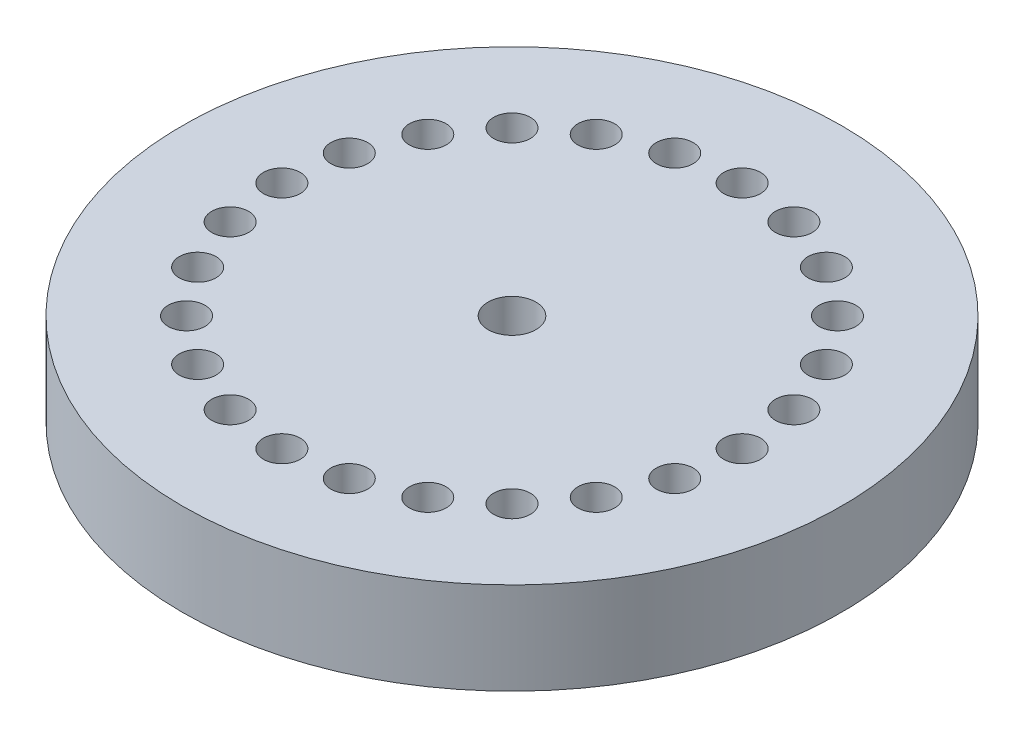
SolidWorks part; units mm, degrees
ref_plane "Front Plane" through (0, 0, 0) normal (0, 0, 1) x (1, 0, 0)
ref_plane "Top Plane" through (0, 0, 0) normal (0, 1, 0) x (1, 0, 0)
ref_plane "Right Plane" through (0, 0, 0) normal (1, 0, 0) x (0, 0, -1)
sketch "Sketch1" plane through (0, 0, 0) normal (0, 1, 0) x (1, 0, 0)
  circle A0 centre (0, 0) radius 20.066 construction
  circle A1 centre (0, 0) radius 45.466
  dimension "D1" = 25.4
extrude "Boss-Extrude1" add sketch "Sketch1" along normal blind 25.4
sketch "Sketch3" plane through (0, 0, 0) normal (0, -1, 0) x (1, 0, 0)
  circle A0 centre (0, 0) radius 20.32
extrude "Cut-Extrude1" cut sketch "Sketch3" against normal blind 12.7
sketch "Sketch4" plane through (0, 0, 0) normal (0, -1, 0) x (1, 0, 0)
  line L0 (0, 0) -> (0, 31.75) construction
  circle A0 centre (0, 31.75) radius 1.778
hole_wizard "CSK for 1/4 Flat Head Machine Screw1" positions "Sketch6" profile "Sketch7" countersink size "1/4" standard "ANSI Inch"
sketch "Sketch6" plane through (0, 25.4, 0) normal (0, 1, 0) x (1, 0, 0)
  point P0 (0, 0)
sketch "Sketch7" plane through (0, 25.4, 0) normal (1, 0, 0) x (0, 0, 1)
  line L0 (0, 0) -> (0, 27.3611)
  line L1 (0, 27.3611) -> (3.2639, 25.4)
  line L2 (3.2639, 25.4) -> (3.2639, 3.6524)
  line L3 (3.2639, 3.6524) -> (6.4389, 0)
  line L5 (6.4389, 0) -> (0, 0)
  line L6 (-3.2639, 3.6524) -> (-6.4389, 0) construction
  line L10 (0, 27.3611) -> (-3.2639, 25.4) construction
  line L11 (0, -6.35) -> (0, 107.95) construction
  dimension "Hole Dia." = 6.5278
  dimension "Hole Depth" = 25.4
  dimension "Near C'Sink Dia." = 12.8778
  dimension "Near C'Sink Angle" = 82
  dimension "Drill Angle" = 118
sketch "Sketch8" plane through (0, 25.4, 0) normal (0, 1, 0) x (1, 0, 0)
  circle A0 centre (0, 0) radius 46.9556
extrude "Cut-Extrude2" cut sketch "Sketch8" against normal blind 12.7
extrude "Cut-Extrude3" cut sketch "Sketch4" against normal through all
sketch "Sketch9" plane through (0, 12.7, 0) normal (0, 1, 0) x (1, 0, 0)
  circle A0 centre (0, -31.75) radius 2.54
extrude "Cut-Extrude4" cut sketch "Sketch9" against normal blind 5.08
pattern_circular "CirPattern1" count 24 every 15 about axis through (0, 0, 0) along (0, 1, 0) of "Cut-Extrude3", "Cut-Extrude4"
sketch "Sketch10" plane through (0, 12.7, 0) normal (0, 1, 0) x (1, 0, 0)
  circle A0 centre (0, 0) radius 22.8348
extrude "Boss-Extrude2" add sketch "Sketch10" against normal blind 5.08
sketch "Sketch11" plane through (0, 12.7, 0) normal (0, 1, 0) x (1, 0, 0)
  circle A0 centre (0, 0) radius 3.302
  dimension "D1" = 6.604
extrude "Cut-Extrude5" cut sketch "Sketch11" against normal through all
